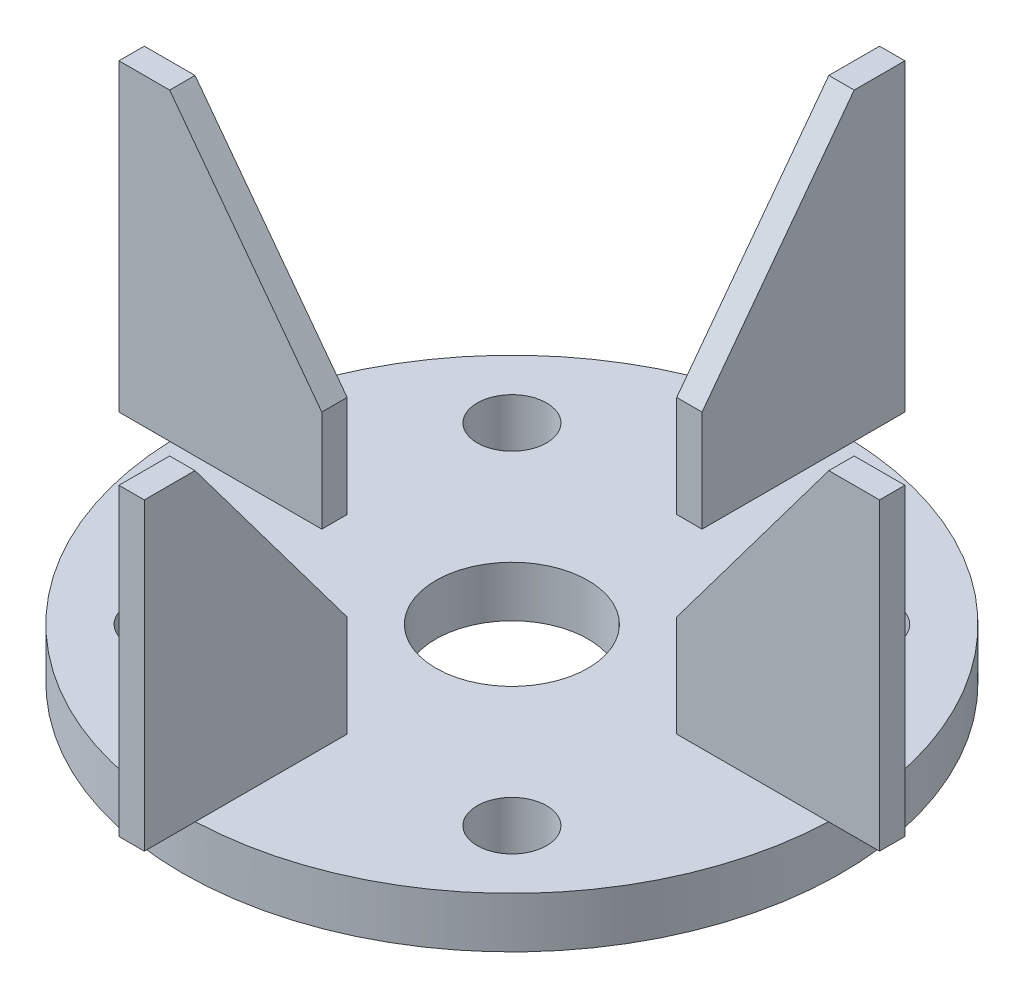
SolidWorks part; units mm, degrees
ref_plane "Front Plane" through (0, 0, 0) normal (0, 0, 1) x (1, 0, 0)
ref_plane "Top Plane" through (0, 0, 0) normal (0, 1, 0) x (1, 0, 0)
ref_plane "Right Plane" through (0, 0, 0) normal (1, 0, 0) x (0, 0, -1)
sketch "Sketch3" plane through (0, 0, 0) normal (0, 1, 0) x (1, 0, 0)
  circle A0 centre (0, 0) radius 82.55
  circle A1 centre (0, 0) radius 19.05
  dimension "D1" = 165.1
  dimension "D2" = 38.1
extrude "Boss-Extrude2" add sketch "Sketch3" along normal blind 12.7
sketch "Sketch5" plane through (0, 0, 0) normal (1, 0, 0) x (0, 0, -1)
  line L2 (-82.55, 88.9) -> (-44.45, 38.1)
  line L3 (-44.45, 38.1) -> (-44.45, 12.7)
  line L4 (82.55, 12.7) -> (-82.55, 12.7) construction
  line L6 (0, 0) -> (0, 86.8043) construction
  line L7 (0, 6.985) -> (0, -6.985) construction
  line L8 (-82.55, 12.7) -> (-95.25, 12.7) construction
  line L9 (-44.45, 12.7) -> (-95.25, 12.7)
  line L10 (-95.25, 12.7) -> (-95.25, 88.9)
  line L12 (-82.55, 88.9) -> (-95.25, 88.9)
  dimension "D1" = 12.7
  dimension "D2" = 25.4
  dimension "D3" = 12.7
  dimension "D4" = 50.8
  dimension "D5" = 76.2
extrude "Boss-Extrude3" add sketch "Sketch5" along normal mid plane 6.35
pattern_circular "CirPattern1" count 4 over 360 about axis through (0, 0, 0) along (0, 1, 0) of "Boss-Extrude3"
sketch "Sketch8" plane through (0, 0, 0) normal (0, 1, 0) x (1, 0, 0)
  line L0 (0, 0) -> (43.68, -43.68) construction
  line L1 (0, 0) -> (0, -47.9733) construction
  line L2 (0, 0) -> (69.3053, 0) construction
  line L3 (0, 0) -> (0, -69.3053) construction
  line L4 (0, 0) -> (-69.3053, 0) construction
  line L5 (0, 0) -> (0, 69.3053) construction
  circle A0 centre (43.68, -43.68) radius 8.6866
  circle A1 centre (-43.68, -43.68) radius 8.6866
  circle A2 centre (-43.68, 43.68) radius 8.6866
  circle A3 centre (43.68, 43.68) radius 8.6866
  point P18 (0, 0)
  dimension "D1" = 45
  dimension "D2" = 4
extrude "Cut-Extrude6" cut sketch "Sketch8" along normal through all
